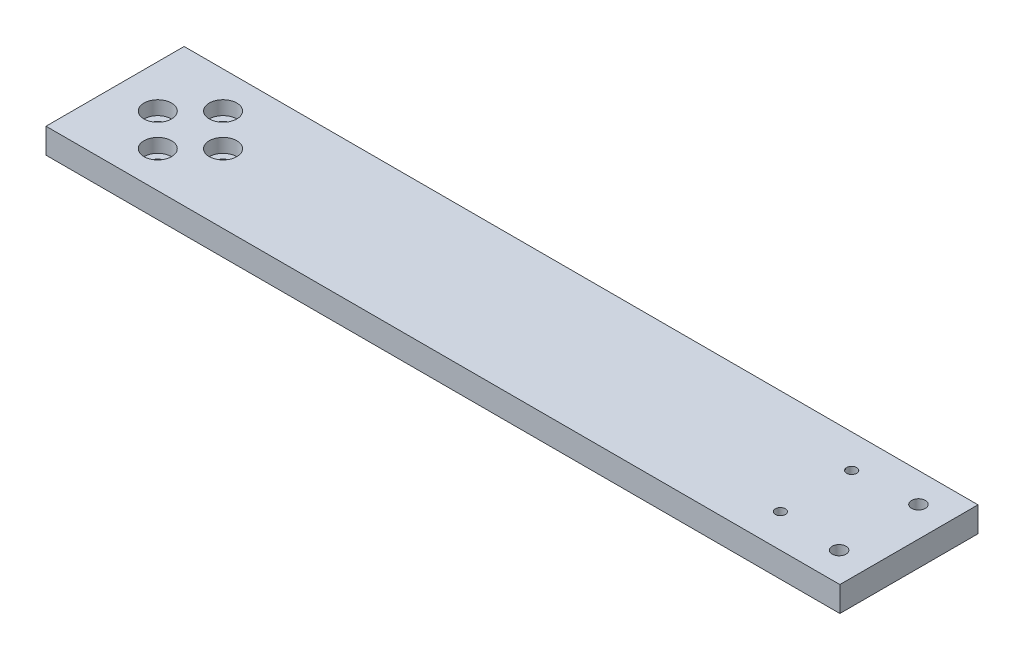
SolidWorks part; units mm, degrees
material "3003 Alloy"
ref_plane "Front Plane" through (0, 0, 0) normal (0, 0, 1) x (1, 0, 0)
ref_plane "Top Plane" through (0, 0, 0) normal (0, 1, 0) x (1, 0, 0)
ref_plane "Right Plane" through (0, 0, 0) normal (1, 0, 0) x (0, 0, -1)
sketch "Sketch1" plane through (0, 0, 0) normal (0, 1, 0) x (1, 0, 0)
  line L1 (0, 0) -> (316.1, 0)
  line L2 (0, 0) -> (0, 55)
  line L3 (0, 55) -> (316.1, 55)
  line L4 (316.1, 0) -> (316.1, 55)
  dimension "D1" = 55
  dimension "D5" = 316.1
extrude "Boss-Extrude1" add sketch "Sketch1" along normal blind 10
sketch "Sketch2" plane through (0, 10, 0) normal (0, 1, 0) x (1, 0, 0)
  line L0 (316.1, 0) -> (316.1, 55) construction
  line L4 (0, 55) -> (316.1, 55) construction
  circle A0 centre (279.1, 13.3) radius 2
  circle A1 centre (279.1, 41.7) radius 2
  circle A2 centre (304.1, 43.3) radius 2.75
  circle A3 centre (304.1, 11.7) radius 2.75
  dimension "D1" = 5.5
  dimension "D8" = 4
  dimension "D2" = 31.6
  dimension "D3" = 28.4
  dimension "D4" = 12
  dimension "D5" = 25
  dimension "D6" = 13.3
  dimension "D7" = 11.7
extrude "Cut-Extrude1" cut sketch "Sketch2" against normal through all
sketch "Sketch3" plane through (0, 0, 0) normal (0, -1, 0) x (1, 0, 0)
  circle A0 centre (304.1, -11.7) radius 5.5
  circle A1 centre (304.1, -43.3) radius 5.5
  dimension "D1" = 11
extrude "Cut-Extrude2" cut sketch "Sketch3" against normal blind 5.5
sketch "Sketch4" plane through (0, 10, 0) normal (0, 1, 0) x (1, 0, 0)
  line L2 (0, 0) -> (0, 55) construction
  line L4 (0, 0) -> (0, 55) construction
  circle A9 centre (30, 27.5) radius 13
  circle A10 centre (17, 27.5) radius 2.75
  circle A11 centre (30, 40.5) radius 2.75
  circle A12 centre (43, 27.5) radius 2.75
  circle A13 centre (30, 14.5) radius 2.75
  point P8 (0, 27.5)
  point P17 (20, 25)
  point P20 (30, 27.5)
  dimension "D3" = 26
  dimension "D4" = 5.5
  dimension "D2" = 30
  dimension "D5" = 4
extrude "Cut-Extrude3" cut sketch "Sketch4" against normal through all
sketch "Sketch5" plane through (0, 10, 0) normal (0, 1, 0) x (1, 0, 0)
  circle A0 centre (17, 27.5) radius 2.75 construction
  circle A1 centre (30, 14.5) radius 2.75 construction
  point P0 (30, 27.5)
  dimension "D2" = 13
  dimension "D1" = 13
sketch "Sketch6" plane through (0, 0, 0) normal (0, -1, 0) x (1, 0, 0)
  circle A2 centre (30, -14.5) radius 4.5
  circle A3 centre (30, -40.5) radius 4.5
  dimension "D1" = 9
  dimension "D2" = 9
extrude "Cut-Extrude4" cut sketch "Sketch6" against normal blind 1.1
sketch "Sketch7" plane through (0, 10, 0) normal (0, 1, 0) x (1, 0, 0)
  circle A0 centre (17, 27.5) radius 5.5
  circle A1 centre (30, 40.5) radius 5.5
  circle A2 centre (43, 27.5) radius 5.5
  circle A3 centre (30, 14.5) radius 5.5
  dimension "D1" = 11
extrude "Cut-Extrude5" cut sketch "Sketch7" against normal blind 5.5
